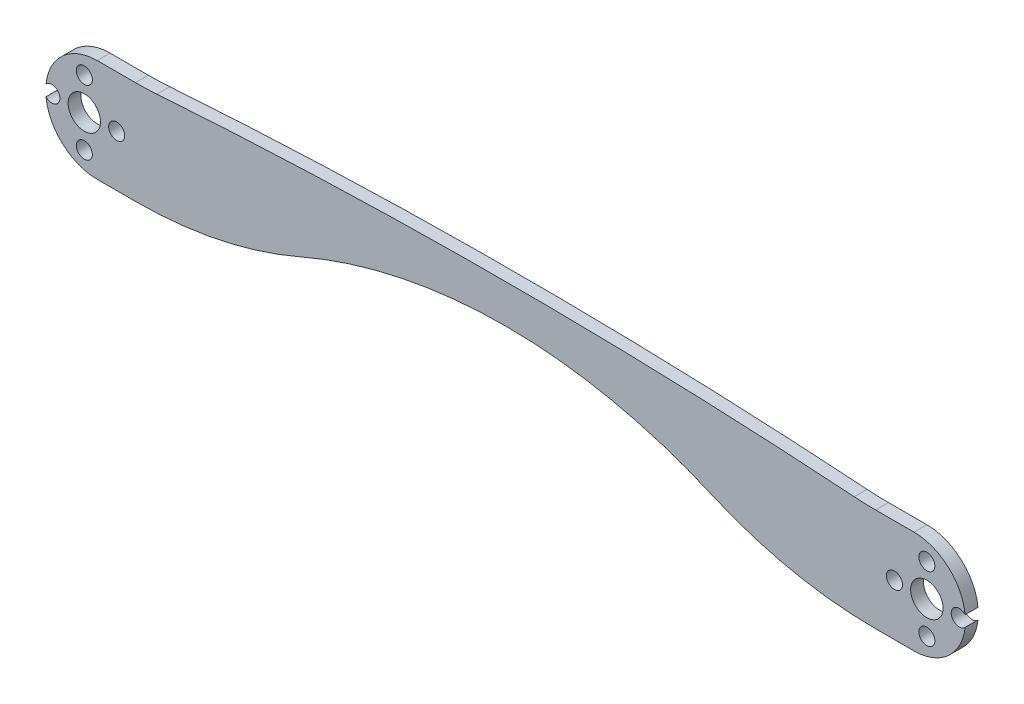
SolidWorks part; units mm, degrees
material "6061-T6 (SS)"
ref_plane "Front Plane" through (0, 0, 0) normal (0, 0, 1) x (1, 0, 0)
ref_plane "Top Plane" through (0, 0, 0) normal (0, 1, 0) x (1, 0, 0)
ref_plane "Right Plane" through (0, 0, 0) normal (1, 0, 0) x (0, 0, -1)
sketch "Sketch2" plane through (0, 0, 0) normal (0, 0, 1) x (1, 0, 0)
  line L0 (0, 0) -> (201.65, 0) construction
  line L1 (100.825, 0) -> (100.825, -120.65) construction
  line L2 (0, 12.7) -> (9.4644, 12.7)
  line L3 (9.4644, -12.7) -> (0, -12.7)
  line L4 (192.1856, 12.7) -> (201.65, 12.7)
  line L5 (201.65, -12.7) -> (192.1856, -12.7)
  line L6 (-902.35, 6.35) -> (49097.65, 6.35) construction
  line L7 (-902.35, 15.875) -> (49097.65, 15.875) construction
  line L8 (-12.7, -1001.3434) -> (-12.7, 48998.6566) construction
  line L9 (214.35, -1001.6608) -> (214.35, 48998.3392) construction
  arc A0 (0, 12.7) -> (0, -12.7) centre (0, 0) ccw
  arc A1 (50.0691, -4.2333) -> (151.5809, -4.2333) centre (100.825, -120.65) cw
  arc A2 (14.7543, 12.8838) -> (186.8957, 12.8838) centre (100.825, -1223.9625) cw
  arc A3 (14.7543, 12.8838) -> (9.4644, 12.7) centre (9.4644, 88.9) cw
  arc A4 (50.0691, -4.2333) -> (9.4644, -12.7) centre (9.4644, 88.9) cw
  arc A5 (186.8957, 12.8838) -> (192.1856, 12.7) centre (192.1856, 88.9) ccw
  arc A6 (151.5809, -4.2333) -> (192.1856, -12.7) centre (192.1856, 88.9) ccw
  arc A7 (201.65, 12.7) -> (201.65, -12.7) centre (201.65, 0) cw
  point P22 (100.825, 6.35)
  dimension "D4" = 127
  dimension "D3" = 19.05
  dimension "D5" = 9.525
  dimension "D6" = 101.6
  dimension "D1" = 227.05
  dimension "D2" = 25.4
extrude "Boss-Extrude1" add sketch "Sketch2" along normal blind 3.175
sketch "Sketch3" plane through (0, 0, 3.175) normal (0, 0, 1) x (1, 0, 0)
  line L0 (-1000, 0) -> (49000, 0) construction
  line L1 (214.35, -1000) -> (214.35, 49000) construction
  line L2 (-12.7, -1000) -> (-12.7, 49000) construction
  line L3 (-3.175, 0) -> (-3.175, 8) construction
  line L4 (204.825, 0) -> (204.825, 8) construction
  circle A0 centre (-3.175, 8) radius 1.9844
  circle A1 centre (-3.175, 0) radius 4
  circle A2 centre (204.825, 0) radius 4
  circle A3 centre (204.825, 8) radius 1.9844
  arc A4 (201.65, -12.7) -> (201.65, 12.7) centre (201.65, 0) ccw construction
  arc A5 (0, 12.7) -> (0, -12.7) centre (0, 0) ccw construction
  circle A6 centre (212.825, 0) radius 1.9844
  circle A7 centre (204.825, -8) radius 1.9844
  circle A8 centre (196.825, 0) radius 1.9844
  circle A9 centre (4.825, 0) radius 1.9844
  circle A10 centre (-3.175, -8) radius 1.9844
  circle A11 centre (-11.175, 0) radius 1.9844
  point P18 (214.35, 0)
  point P24 (-12.7, 0)
  dimension "D1" = 9.525
  dimension "D2" = 90
  dimension "D4" = 8
  dimension "D5" = 3.9688
  dimension "D3" = 90
  dimension "D6" = 8
  dimension "D7" = 8
  dimension "D8" = 9.525
  dimension "D9" = 4
  dimension "D10" = 4
extrude "Cut-Extrude1" cut sketch "Sketch3" against normal through all
